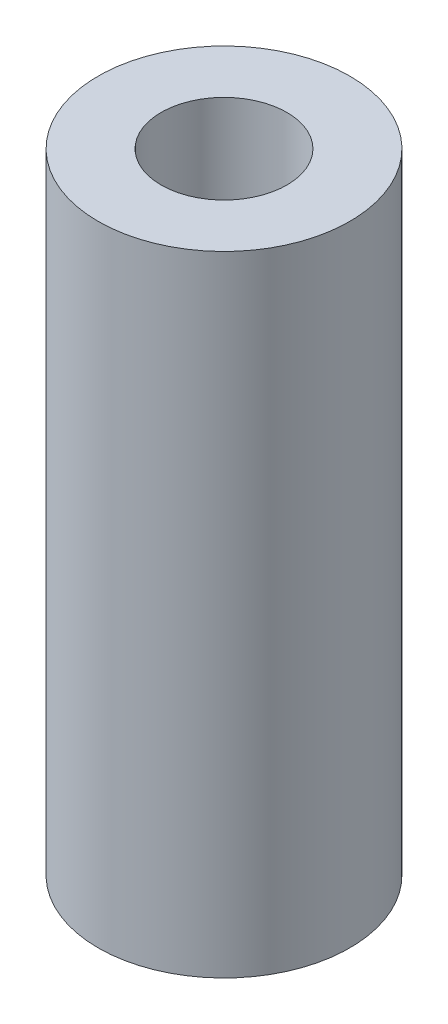
SolidWorks part; units mm, degrees
material "Stahl"
ref_plane "Vorne" through (0, 0, 0) normal (0, 0, 1) x (1, 0, 0)
ref_plane "Oben" through (0, 0, 0) normal (0, 1, 0) x (1, 0, 0)
ref_plane "Rechts" through (0, 0, 0) normal (1, 0, 0) x (0, 0, -1)
sketch "Skizze1" plane through (0, 0, 0) normal (0, 1, 0) x (1, 0, 0)
  circle A0 centre (0, 0) radius 5
  circle A1 centre (0, 0) radius 2.5
  dimension "D1" = 10
  dimension "D2" = 5
extrude "Aufsatz-Linear austragen1" add sketch "Skizze1" along normal blind 25
